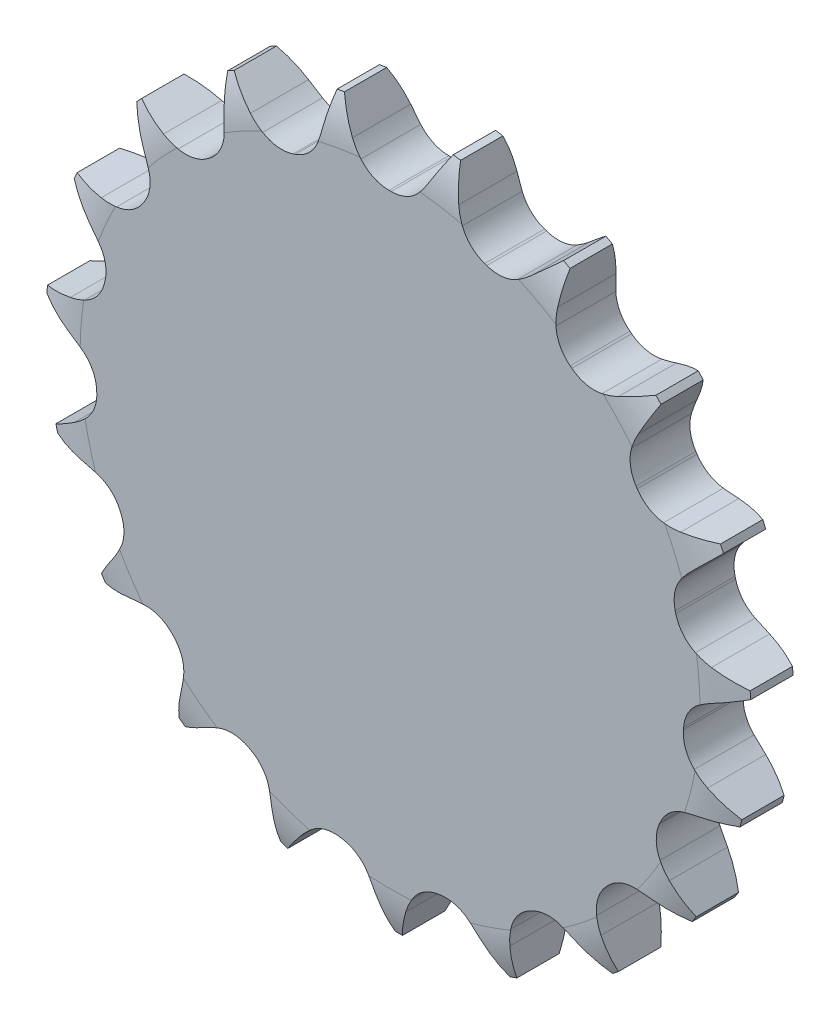
SolidWorks part; units mm, degrees
ref_plane "Přední rovina" through (0, 0, 0) normal (0, 0, 1) x (1, 0, 0)
ref_plane "Horní rovina" through (0, 0, 0) normal (0, 1, 0) x (1, 0, 0)
ref_plane "Pravá rovina" through (0, 0, 0) normal (1, 0, 0) x (0, 0, -1)
sketch "Skica1" plane through (0, 0, 0) normal (1, 0, 0) x (0, 0, -1)
  line L0 (0, 0) -> (-87.9985, 0) construction
  line L1 (0, 0) -> (33.0198, 0) construction
  line L2 (0, 0) -> (0, 111.4215) construction
  line L3 (0, 0) -> (0, -124.7595) construction
  line L4 (0, 0) -> (0, 36.1288)
  line L5 (-1.0212, 41.1326) -> (-5.9538, 41.1326)
  line L6 (-6.975, 36.1288) -> (-6.975, 0)
  line L7 (0, 0) -> (-6.975, 0)
  arc A0 (-1.0212, 41.1326) -> (0, 36.1288) centre (-12.77, 36.1288) cw
  arc A1 (-5.9538, 41.1326) -> (-6.975, 36.1288) centre (5.795, 36.1288) ccw
  point P3 (-1.0212, 41.1326)
  point P10 (-5.9538, 41.1326)
revolve "Rotovat2" add sketch "Skica1" angle 360 about L0
sketch "Skica2" plane through (0, 0, 0) normal (0, 0, 1) x (1, 0, 0)
  line L0 (0, 0) -> (-52.7395, 0) construction
  line L1 (0, 0) -> (53.9794, 0) construction
  line L2 (0, 0) -> (0, 54.5784) construction
  line L3 (0.127, 54.5784) -> (0.127, -5.0851) construction
  line L4 (4.4767, 37.4053) -> (7.4129, 42.4909)
  line L5 (-4.4767, 37.4053) -> (-7.4129, 42.4909)
  line L6 (-0.127, 34.3246) -> (0.127, 34.3246)
  circle A0 centre (0, 0) radius 38.5796 construction
  arc A2 (3.3964, 35.8564) -> (4.4767, 37.4053) centre (-5.1041, 42.9368) ccw
  arc A3 (0.127, 34.3246) -> (3.3964, 35.8564) centre (0.127, 38.5796) ccw
  arc A4 (-0.127, 34.3246) -> (-3.3964, 35.8564) centre (-0.127, 38.5796) cw
  arc A5 (-3.3964, 35.8564) -> (-4.4767, 37.4053) centre (5.1041, 42.9368) cw
  arc A6 (7.4129, 42.4909) -> (-7.4129, 42.4909) centre (0, 0) ccw
  arc A7 (-43.1326, 0) -> (43.1326, 0) centre (0, 0) ccw
  point P8 (0.127, 38.5796)
  point P14 (0.127, 34.3246)
  point P15 (3.3964, 35.8564)
extrude "Odebrat vysunutím1" cut sketch "Skica2" along normal through all contours L4 A6 L5 A5 A4 L6 A3 A2
pattern_circular "Kruhové pole1" count 19 over 360 about axis through (0, 0, 0) along (0, 0, 1) of "Odebrat vysunutím1"
equation "\"d1\"= 8.51'průměr válečku"
equation "\"t\"= 12.7'rozteč řetězu"
equation "\"z\" = 19'počet zubů"
equation "\"b1\"= 7.75'vnitřní šířka řetězu"
equation "\"D1@Skica2\"= \"t\" / sin ( 180 / \"z\" ) 'průměr roztečné kružnice"
equation "\"c\"= 1'zač.R zubu od boku"
equation "\"D4@Skica1\"= \"d1\" * 0.12'vzdál.R od boku zubu"
equation "\"D2@Skica1\"= \"b1\" * 0.9'šířa zubu"
equation "\"D2@Skica2\"= \"t\" * 0.02 / 2'vzdálenost středu R1 od osy"
equation "\"D4@Skica2\"= \"d1\" * 1.3'navazující poloměr"
equation "\"D5@Skica2\"= \"d1\" * 0.18'Rádius R1 od horizont osy"
equation "\"D6@Skica2\"= \"D1@Skica2\" / 2'vzdál.středu R1 od osy kola"
equation "\"D7@Skica2\"= 30'úhel rozevření zubu/2"
equation "\"D1@Skica1\"= \"D1@Skica2\" + ( 0.6 * \"d1\" )'průměr hlavové kružnice"
equation "\"D8@Skica2\"= \"D1@Skica1\" + 4'pomoc.prům.pro ubrání zubu"
equation "\"D3@Skica2\"= ( \"D1@Skica2\" - \"d1\" ) / 2 'poloměr dna zubu"
equation "\"D1@Kruhové pole1\" = \"z\"'počet zubů"
